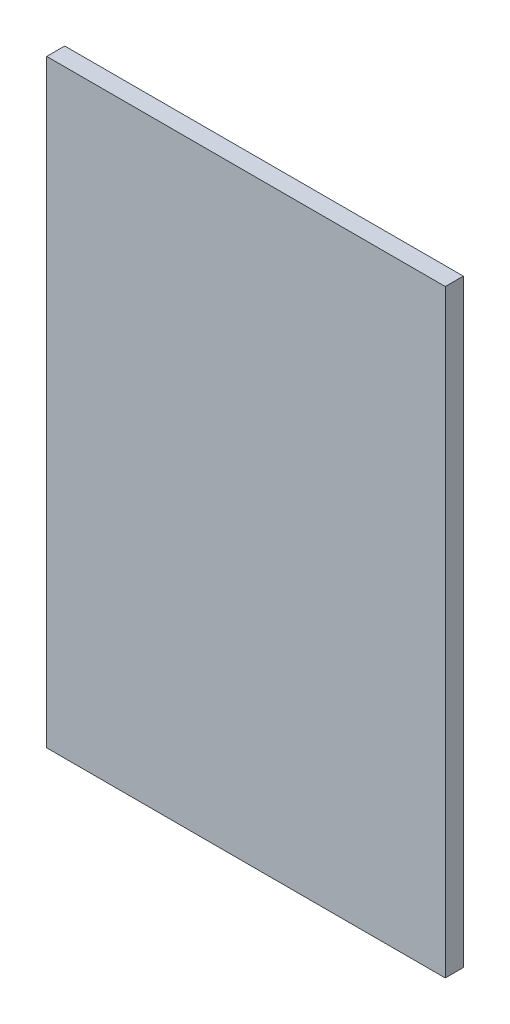
SolidWorks part; units mm, degrees
ref_plane "Front Plane" through (0, 0, 0) normal (0, 0, 1) x (1, 0, 0)
ref_plane "Top Plane" through (0, 0, 0) normal (0, 1, 0) x (1, 0, 0)
ref_plane "Right Plane" through (0, 0, 0) normal (1, 0, 0) x (0, 0, -1)
sketch "Sketch1" plane through (0, 0, 0) normal (0, 0, 1) x (1, 0, 0)
  line L1 (199, -299) -> (-199, -299)
  line L2 (199, -299) -> (199, 299)
  line L3 (199, 299) -> (-199, 299)
  line L4 (-199, -299) -> (-199, 299)
  line L5 (199, -299) -> (-199, 299) construction
  line L6 (199, 299) -> (-199, -299) construction
  point P0 (0, 0)
  dimension "D1" = 598
  dimension "D2" = 398
extrude "Boss-Extrude1" add sketch "Sketch1" along normal blind 18
equation "\"H_DSP\"=18"
equation "\"D1@Boss-Extrude1\"=\"H_DSP\""
